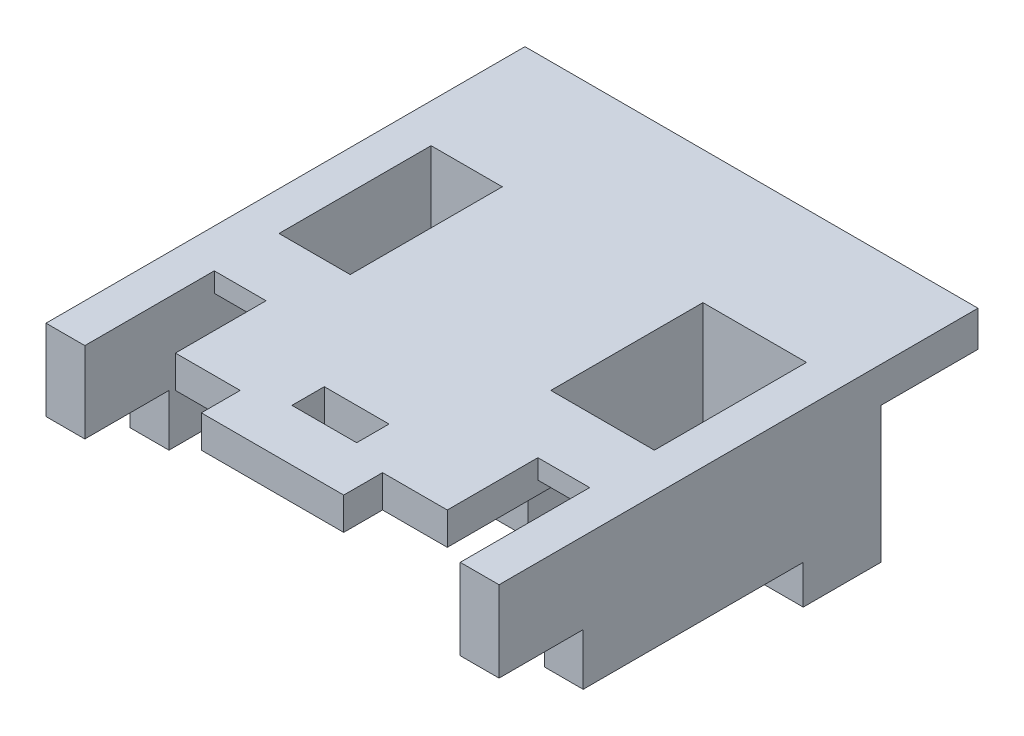
SolidWorks part; units mm, degrees
material "PBT General Purpose"
ref_plane "Front Plane" through (0, 0, 0) normal (0, 0, 1) x (1, 0, 0)
ref_plane "Top Plane" through (0, 0, 0) normal (0, 1, 0) x (1, 0, 0)
ref_plane "Right Plane" through (0, 0, 0) normal (1, 0, 0) x (0, 0, -1)
sketch "Sketch1" plane through (0, 0, 0) normal (0, 1, 0) x (1, 0, 0)
  line L0 (29, -29.5) -> (35, -29.5)
  line L1 (-35, 29.5) -> (35, 29.5)
  line L2 (-35, 29.5) -> (-35, -29.5)
  line L3 (-35, -29.5) -> (-29, -29.5)
  line L4 (35, 29.5) -> (35, -29.5)
  line L5 (-29, 24) -> (29, 24)
  line L6 (-29, 24) -> (-29, -29.5)
  line L8 (29, 24) -> (29, -29.5)
  point P8 (0, 24)
  point P10 (-35, 0)
  dimension "D1" = 70
  dimension "D2" = 59
  dimension "D3" = 6
  dimension "D4" = 5.5
  dimension "D5" = 6
extrude "Boss-Extrude1" add sketch "Sketch1" along normal blind 20.5
sketch "Sketch2" plane through (0, 0, 0) normal (0, -1, 0) x (1, 0, 0)
  line L0 (35, 29.5) -> (35, -29.5) construction
  line L1 (29, 29.5) -> (35, 29.5)
  line L2 (29, 29.5) -> (29, 16.5)
  line L3 (29, 16.5) -> (35, 16.5)
  line L4 (35, 29.5) -> (35, 16.5)
  line L5 (0, -1000) -> (0, 49000) construction
  line L6 (-29, -24) -> (29, -24) construction
  line L12 (-29, 16.5) -> (-35, 16.5)
  line L13 (-35, 29.5) -> (-35, 16.5)
  line L14 (-29, 29.5) -> (-35, 29.5)
  line L15 (-29, 29.5) -> (-29, 16.5)
  dimension "D1" = 13
extrude "Cut-Extrude1" cut sketch "Sketch2" against normal blind 8
sketch "Sketch3" plane through (0, 20.5, 0) normal (0, 1, 0) x (1, 0, 0)
  line L0 (-29, -29.5) -> (-29, 24) construction
  line L1 (-14, 24) -> (9, 24)
  line L2 (-14, 24) -> (-14, 1)
  line L3 (-14, 1) -> (9, 1)
  line L4 (9, 24) -> (9, 1)
  line L6 (-29, 24) -> (29, 24) construction
  dimension "D1" = 23
  dimension "D2" = 23
  dimension "D3" = 15
extrude "Boss-Extrude2" add sketch "Sketch3" against normal offset from surface (6 mm away) 14.5 separate body up to face at (0, 0, -5.125)
sketch "Sketch4" plane through (0, 20.5, 0) normal (0, 1, 0) x (1, 0, 0)
  line L0 (-18, 24) -> (-18, -3)
  line L1 (-29, 24) -> (29, 24) construction
  line L2 (-18, -3) -> (13, -3)
  line L3 (13, -3) -> (13, 24)
  line L4 (-14, 24) -> (-14, 1)
  line L5 (-14, 1) -> (9, 1)
  line L6 (9, 1) -> (9, 24)
  line L7 (9, 24) -> (-14, 24)
  line L8 (-14, 24) -> (-14, 1)
  line L9 (-14, 1) -> (9, 1)
  line L10 (9, 1) -> (9, 24)
  line L11 (9, 24) -> (-14, 24)
  line L12 (13, 24) -> (-18, 24)
  line M12 (-29, 24) -> (29, 24)
  dimension "D2" = 4
  dimension "D3" = 4
  dimension "D4" = 4
  dimension "D1" = 0
extrude "Boss-Extrude4" add sketch "Sketch4" against normal offset from surface (18 mm away) 12 contours L2 L3 L0 L11 L10 L9 L8 M12 up to face at (-2.5, 14.5, -12.5) offset beyond the face yes
sketch "Sketch5" plane through (0, 0, 0) normal (0, -1, 0) x (1, 0, 0)
  line L0 (35, -29.5) -> (-35, -29.5) construction
  line L1 (-6.95, -24) -> (-9.55, -24)
  line L2 (-6.95, -24) -> (-6.95, -29.5)
  line L3 (-6.95, -29.5) -> (-9.55, -29.5)
  line L4 (-9.55, -24) -> (-9.55, -29.5)
  line L5 (-29, -24) -> (29, -24) construction
  line L7 (-9.55, -1) -> (-6.95, -1)
  line L8 (-9.55, -1) -> (-9.55, 3)
  line L9 (-9.55, 3) -> (-6.95, 3)
  line L10 (-6.95, -1) -> (-6.95, 3)
  line L13 (-18, -1) -> (-14, -1)
  line L14 (-18, -1) -> (-18, -16)
  line L15 (-18, -16) -> (-14, -16)
  line L16 (-14, -1) -> (-14, -16)
  line L17 (-14, -1) -> (-14, -24) construction
  line L18 (9, -1) -> (-14, -1) construction
  line L19 (2.55, 3) -> (4.55, 3)
  line L20 (2.55, 3) -> (2.55, -1)
  line L21 (2.55, -1) -> (4.55, -1)
  line L22 (4.55, 3) -> (4.55, -1)
  line L26 (9, -1) -> (-14, -1) construction
  line L27 (13, 3) -> (-18, 3) construction
  line L28 (-18, 3) -> (-18, -24) construction
  dimension "D1" = 2
  dimension "D2" = 9.5
  dimension "D3" = 15
  dimension "D4" = 2.6
  dimension "D5" = 4.45
extrude "Cut-Extrude2" cut sketch "Sketch5" against normal up to surface (14.5 mm away) up to face at (-2.5, 14.5, -12.5)
sketch "Sketch9" plane through (0, 0, -29.5) normal (0, 0, -1) x (-1, 0, 0)
  line L0 (35, 20.5) -> (35, 0) construction
  line L1 (-35, 20.5) -> (35, 20.5)
  line L2 (-35, 20.5) -> (-35, 15)
  line L3 (-35, 15) -> (35, 15)
  line L4 (35, 20.5) -> (35, 15)
  dimension "D1" = 5.5
extrude "Boss-Extrude6" add sketch "Sketch9" along normal blind 15
sketch "Sketch10" plane through (0, 15, 0) normal (0, -1, 0) x (1, 0, 0)
  line L1 (35, -44.5) -> (-35, -44.5) construction
  line L3 (35, -29.5) -> (-35, -29.5) construction
  line L4 (11.5, -29.5) -> (-11.5, -29.5)
  line L6 (-14.5, -37) -> (14.5, -37)
  line L7 (-14.5, -37) -> (-11.5, -29.5)
  line L8 (14.5, -37) -> (11.5, -29.5)
  point P5 (0, -44.5)
  point P6 (0, -37)
  dimension "D1" = 23
  dimension "D2" = 7.5
  dimension "D3" = 3
  dimension "D4" = 3
extrude "Boss-Extrude7" add sketch "Sketch10" along normal blind 7.5
sketch "Sketch11" plane through (0, 0, -29.5) normal (0, 0, -1) x (-1, 0, 0)
  line L0 (-7.5, 0) -> (7.5, 0) construction
  line L1 (-35, 0) -> (6.95, 0) construction
  line L2 (-7.5, 2.5) -> (7.5, 2.5)
  line L3 (-7.5, -2.5) -> (7.5, -2.5)
  line L4 (14.5, 7.5) -> (-14.5, 7.5) construction
  arc A0 (-7.5, 2.5) -> (-7.5, -2.5) centre (-7.5, 0) ccw
  arc A1 (7.5, -2.5) -> (7.5, 2.5) centre (7.5, 0) ccw
  point P4 (0, 0)
  point P12 (0, 7.5)
  dimension "D2" = 2.5
  dimension "D1" = 15
extrude "Cut-Extrude3" cut sketch "Sketch11" against normal up to surface (5.5 mm away) up to face at (11.0125, 9.375, -24)
sketch "Sketch12" plane through (0, 0, 0) normal (0, -1, 0) x (1, 0, 0)
  line L0 (35, -17.5) -> (29, -17.5)
  line L1 (23, -24) -> (23, -29.5)
  line L2 (-23, -24) -> (-23, -29.5)
  line L3 (-29, -17.5) -> (-35, -17.5)
  line L6 (29, -24) -> (10, -24)
  line L7 (10, -24) -> (10, -29.5)
  line L8 (10, -29.5) -> (35, -29.5)
  line L9 (35, -29.5) -> (35, 16.5)
  line L10 (35, 16.5) -> (29, 16.5)
  line L11 (29, 16.5) -> (29, -24)
  line L12 (29, -24) -> (23, -24)
  line L14 (23, -29.5) -> (35, -29.5)
  line L15 (35, -29.5) -> (35, -17.5)
  line L17 (29, -17.5) -> (29, -24)
  line L18 (-35, -29.5) -> (-10, -29.5)
  line L19 (-10, -29.5) -> (-10, -24)
  line L20 (-10, -24) -> (-29, -24)
  line L21 (-29, -24) -> (-29, 16.5)
  line L22 (-29, 16.5) -> (-35, 16.5)
  line L23 (-35, 16.5) -> (-35, -29.5)
  line L24 (-35, -29.5) -> (-23, -29.5)
  line L26 (-23, -24) -> (-29, -24)
  line L27 (-29, -24) -> (-29, -17.5)
  line L29 (-35, -17.5) -> (-35, -29.5)
  dimension "D3" = 12
  dimension "D4" = 12
  dimension "D5" = 12
  dimension "D6" = 12
  dimension "D1" = 0
  dimension "D2" = 0
extrude "Boss-Extrude8" add sketch "Sketch12" along normal blind 6
sketch "Sketch14" plane through (35, 0, 0) normal (1, 0, 0) x (0, 0, -1)
  line L0 (-29.5, 20.5) -> (44.5, 20.5) construction
  line L1 (-9.5, 20.5) -> (0.5, 20.5)
  line L2 (-9.5, 20.5) -> (-9.5, 17.5)
  line L3 (-6.5, 15.5) -> (-2.5, 15.5)
  line L4 (0.5, 20.5) -> (0.5, 18.5)
  line L5 (-29.5, 20.5) -> (-29.5, 8) construction
  line L6 (-9.5, 17.5) -> (-6.5, 15.5)
  line L7 (-2.5, 15.5) -> (0.5, 18.5)
  point P1 (0.5, 15.5)
  point P2 (-9.5, 15.5)
  dimension "D1" = 30
  dimension "D2" = 10
  dimension "D3" = 5
  dimension "D4" = 2
  dimension "D5" = 3
extrude "Boss-Extrude10" add sketch "Sketch14" against normal up to surface (58 mm away) from surface at -6 up to face at (-29, 5.625, 1.125) starting at face at (29, 5.625, 1.125)
sketch "Sketch15" plane through (35, 0, 0) normal (1, 0, 0) x (0, 0, -1)
  line L1 (-9.5, 20.5) -> (0.5, 20.5)
  line L2 (-9.5, 20.5) -> (-9.5, 15.5)
  line L3 (-9.5, 15.5) -> (0.5, 15.5)
  line L4 (0.5, 20.5) -> (0.5, 15.5)
extrude "Boss-Extrude11" add sketch "Sketch15" against normal blind 42 from offset 14 offset against normal yes
sketch "Sketch16" plane through (0, 0, 9.5) normal (0, 0, 1) x (1, 0, 0)
  line L0 (-29, 20.5) -> (29, 20.5) construction
  line L1 (-21, 15.5) -> (21, 15.5)
  line L2 (-21, 15.5) -> (-21, 20.5)
  line L3 (-21, 20.5) -> (21, 20.5)
  line L4 (21, 15.5) -> (21, 20.5)
  line L5 (21, 17.5) -> (21, 15.5) construction
extrude "Boss-Extrude12" add sketch "Sketch16" along normal up to surface (20 mm away) up to face at (32, 14.25, 29.5)
sketch "Sketch17" plane through (0, 20.5, 0) normal (0, 1, 0) x (1, 0, 0)
  line L0 (-21, -29.5) -> (21, -29.5) construction
  line L1 (-21, -29.5) -> (-11, -29.5)
  line L2 (-21, -29.5) -> (-21, -23.5)
  line L3 (-21, -23.5) -> (-11, -23.5)
  line L4 (-11, -29.5) -> (-11, -23.5)
  line L5 (21, -29.5) -> (11, -29.5)
  line L6 (21, -29.5) -> (21, -23.5)
  line L7 (21, -23.5) -> (11, -23.5)
  line L8 (11, -29.5) -> (11, -23.5)
  line L9 (-5, -21.5) -> (5, -21.5)
  line L10 (-5, -21.5) -> (-5, -16.5)
  line L11 (-5, -16.5) -> (5, -16.5)
  line L12 (5, -21.5) -> (5, -16.5)
  point P16 (0, -21.5)
  point P17 (0, -29.5)
  dimension "D1" = 6
  dimension "D2" = 6
  dimension "D3" = 10
  dimension "D4" = 10
  dimension "D5" = 8
  dimension "D6" = 10
  dimension "D7" = 5
extrude "Cut-Extrude4" cut sketch "Sketch17" against normal up to next
equation "\"body_height\"= 41mm"
equation "\"D1@Boss-Extrude1\"=\"body_height\" / 2"
equation "\"D1@Boss-Extrude2\"=12+2.5"
